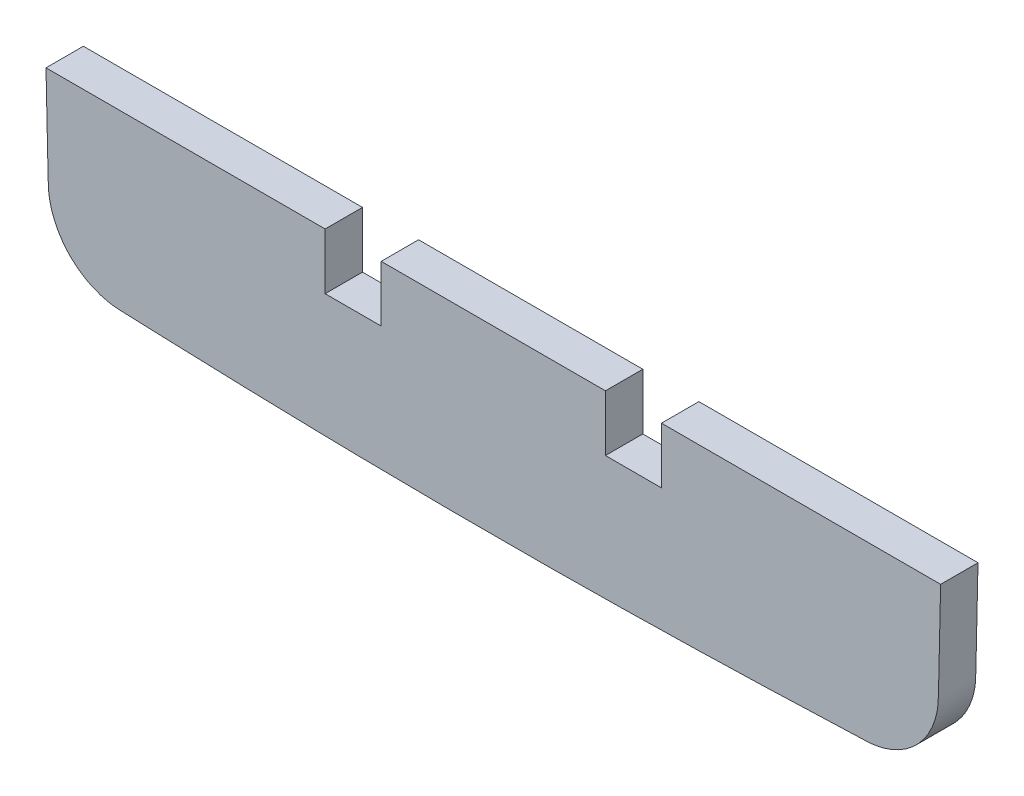
SolidWorks part; units mm, degrees
material "Beech"
ref_plane "Front Plane" through (0, 0, 0) normal (0, 0, 1) x (1, 0, 0)
ref_plane "Top Plane" through (0, 0, 0) normal (0, 1, 0) x (1, 0, 0)
ref_plane "Right Plane" through (0, 0, 0) normal (1, 0, 0) x (0, 0, -1)
sketch "Sketch1" plane through (0, 0, 0) normal (0, 0, 1) x (1, 0, 0)
  line L0 (0, 0) -> (63.5, 0) construction
  line L1 (63.5, 0) -> (63.5, 63.2554) construction
  line L2 (63.5, 0) -> (124.7026, 0) construction
  line L3 (63.5, 0) -> (63.5, -62.7074) construction
  line L4 (2.6999, -38.1) -> (124.3001, -38.1)
  line L5 (86.36, -38.1) -> (86.36, -45.72)
  line L6 (48.26, -38.1) -> (40.64, -38.1)
  line L7 (48.26, -38.1) -> (48.26, -45.72)
  line L8 (48.26, -45.72) -> (40.64, -45.72)
  line L9 (40.64, -38.1) -> (40.64, -45.72)
  line L10 (78.74, -45.72) -> (86.36, -45.72)
  line L11 (78.74, -38.1) -> (78.74, -45.72)
  line L12 (78.74, -38.1) -> (86.36, -38.1)
  spline S0 degree 3 poles (63.5, 63.2554) (72.1161, 63.2554) (81.1425, 63.1552) (90.6287, 62.9375) (95.3717, 62.8286) (100.2303, 62.6907) (105.2149, 62.5234) (107.7072, 62.4398) (110.2311, 62.3489) (112.7885, 62.2508) (113.1082, 62.2385) (113.4283, 62.2262) (113.7491, 62.2137) (113.9094, 62.2074) (114.0699, 62.2012) (114.3912, 62.1886) (114.5519, 62.1824) (114.7135, 62.1709) (115.3597, 62.1249) (116.0151, 62.0144) (117.3109, 61.6584) (117.9513, 61.4122) (118.567, 61.0968) (118.8749, 60.9391) (119.1765, 60.7646) (119.4698, 60.5741) (119.6164, 60.4788) (119.761, 60.3796) (119.9743, 60.225) (120.0448, 60.1725) (120.1496, 60.0923) (120.1843, 60.0654) (120.2362, 60.0246) (120.2535, 60.0109) (120.2794, 59.9904) (120.288, 59.9835) (120.3051, 59.9697) (120.3153, 59.9615) (120.3223, 59.9559) (120.7681, 59.5962) (121.1871, 59.1957) (121.9526, 58.3221) (122.2998, 57.8498) (122.9105, 56.8518) (123.1741, 56.3262) (123.6048, 55.2405) (123.7722, 54.6805) (124.011, 53.546) (124.0824, 52.9716) (124.1056, 52.4006) (124.1115, 52.2579) (124.1138, 52.1155) (124.1201, 51.83) (124.1233, 51.6871) (124.1265, 51.544) (124.1329, 51.2578) (124.1392, 50.9708) (124.1455, 50.683) (124.1707, 49.532) (124.1954, 48.3687) (124.2196, 47.1932) (124.268, 44.8421) (124.3143, 42.442) (124.3577, 39.9928) (124.3794, 38.7682) (124.4003, 37.5313) (124.4205, 36.2822) (124.4306, 35.6576) (124.4405, 35.03) (124.4502, 34.3993) (124.455, 34.0839) (124.4598, 33.7678) (124.4645, 33.4509) (124.4669, 33.2925) (124.4693, 33.1339) (124.4728, 32.8956) (124.4739, 32.8162) (124.4757, 32.6969) (124.4763, 32.6572) (124.4771, 32.5975) (124.4774, 32.5776) (124.4778, 32.5478) (124.478, 32.5378) (124.4782, 32.5229) (124.4783, 32.5179) (124.4784, 32.508) (124.4785, 32.5018) (124.4786, 32.498) (124.5348, 28.6259) (124.5877, 24.3084) (124.6285, 19.5453) (124.6489, 17.1637) (124.6662, 14.6708) (124.6791, 12.0667) (124.6856, 10.7646) (124.6909, 9.4347) (124.6949, 8.0771) (124.6969, 7.3983) (124.6986, 6.7125) (124.7, 6.0198) (124.7007, 5.6734) (124.7012, 5.3253) (124.7017, 4.9755) (124.702, 4.8006) (124.7022, 4.6253) (124.7025, 4.3616) (124.7026, 4.2736) (124.7028, 4.1414) (124.7028, 4.0974) (124.7029, 4.0312) (124.7029, 4.0091) (124.7029, 3.976) (124.7029, 3.965) (124.703, 3.9485) (124.703, 3.9429) (124.703, 3.9347) (124.703, 3.9319) (124.703, 3.9264) (124.703, 3.9214) (124.703, 3.9209) (124.7035, 3.3699) (124.7052, 1.9034) (124.7021, -0.4784) (124.7005, -1.6693) (124.6976, -3.089) (124.6919, -4.7373) (124.689, -5.5615) (124.6855, -6.4429) (124.681, -7.3814) (124.6787, -7.8506) (124.6762, -8.3342) (124.6735, -8.832) (124.6721, -9.0809) (124.6706, -9.3334) (124.6691, -9.5894) (124.6684, -9.7174) (124.6676, -9.8463) (124.6664, -10.0411) (124.666, -10.1062) (124.6654, -10.2042) (124.6652, -10.2369) (124.6649, -10.2861) (124.6648, -10.3025) (124.6646, -10.3272) (124.6646, -10.3354) (124.6645, -10.3477) (124.6645, -10.3518) (124.6644, -10.36) (124.6644, -10.3654) (124.6644, -10.3683) (124.6461, -13.2676) (124.6231, -15.9079) (124.5987, -18.2892) (124.5864, -19.4799) (124.5738, -20.6058) (124.5611, -21.667) (124.5548, -22.1976) (124.5485, -22.7121) (124.5421, -23.2103) (124.539, -23.4595) (124.5358, -23.7046) (124.5327, -23.9456) (124.5311, -24.0661) (124.5295, -24.1857) (124.5272, -24.3634) (124.5264, -24.4224) (124.5252, -24.5105) (124.5248, -24.5399) (124.5242, -24.5837) (124.524, -24.5983) (124.5237, -24.6202) (124.5236, -24.6275) (124.5235, -24.6384) (124.5235, -24.6421) (124.5234, -24.6494) (124.5233, -24.6513) (124.5233, -24.6567) (124.4496, -30.1549) (124.3589, -35.2827) (124.261, -40.0405) (124.2121, -42.4195) (124.1612, -44.7059) (124.1096, -46.9002) (124.0838, -47.9973) (124.0578, -49.0713) (124.0316, -50.1224) (124.0186, -50.6479) (124.0069, -51.1674) (123.9924, -51.6816) (123.9851, -51.9387) (123.9681, -52.1959) (123.9415, -52.4522) (123.9282, -52.5804) (123.9125, -52.7083) (123.8854, -52.8997) (123.8758, -52.9634) (123.8605, -53.0588) (123.8552, -53.0905) (123.8471, -53.1382) (123.8444, -53.154) (123.8402, -53.1778) (123.8388, -53.1857) (123.8367, -53.1976) (123.836, -53.2016) (123.8346, -53.2095) (123.8341, -53.2123) (123.8332, -53.2174) (123.7148, -53.876) (123.5319, -54.5285) (123.0366, -55.7896) (122.7234, -56.3983) (121.985, -57.5417) (121.5599, -58.0765) (120.6162, -59.0438) (120.0977, -59.4763) (118.9995, -60.2267) (118.4198, -60.5446) (117.2296, -61.0543) (116.6192, -61.2465) (116.0078, -61.3797) (115.7021, -61.4462) (115.3961, -61.498) (114.7871, -61.5729) (114.4845, -61.5936) (114.1842, -61.6057) (113.5835, -61.6298) (112.9862, -61.6534) (112.3923, -61.6767) (110.0169, -61.7696) (107.6958, -61.8555) (105.4273, -61.9346) (104.293, -61.9741) (103.1719, -62.0119) (102.0638, -62.048) (101.5098, -62.0661) (100.9589, -62.0837) (100.4113, -62.1009) (100.1375, -62.1095) (99.8646, -62.118) (99.5924, -62.1264) (99.4563, -62.1306) (99.3204, -62.1348) (99.1168, -62.141) (99.049, -62.1431) (98.9474, -62.1462) (98.9136, -62.1472) (98.8628, -62.1487) (98.8459, -62.1492) (98.8205, -62.15) (98.812, -62.1503) (98.7951, -62.1508) (98.7883, -62.151) (98.7782, -62.1513) (93.6295, -62.3071) (88.6269, -62.4294) (83.759, -62.5187) (81.3251, -62.5633) (78.9249, -62.5997) (76.5574, -62.6282) (75.3736, -62.6425) (74.198, -62.6547) (73.0305, -62.6651) (72.4468, -62.6702) (71.8651, -62.6749) (71.2853, -62.6791) (70.9955, -62.6812) (70.7061, -62.6832) (70.4172, -62.685) (70.2728, -62.686) (70.1285, -62.6869) (69.9122, -62.6882) (69.8401, -62.6886) (69.6961, -62.6894) (69.6254, -62.6898) (69.5521, -62.6903) (67.2067, -62.7035) (64.8341, -62.7093) (60.0428, -62.7045) (57.6274, -62.694) (52.7555, -62.6564) (50.2989, -62.6292) (47.8205, -62.5936) (46.5814, -62.5758) (45.3367, -62.5559) (44.0865, -62.5339) (43.4614, -62.5229) (42.8349, -62.5113) (42.207, -62.4992) (41.893, -62.4932) (41.5787, -62.487) (41.264, -62.4807) (41.1067, -62.4776) (40.9493, -62.4744) (40.713, -62.4696) (40.6342, -62.468) (40.516, -62.4655) (40.4766, -62.4647) (40.4175, -62.4635) (40.3978, -62.4631) (40.3584, -62.4623) (40.3365, -62.4618) (40.3189, -62.4615) (35.814, -62.3677) (31.1356, -62.2449) (26.2735, -62.091) (23.8424, -62.014) (21.3654, -61.9294) (18.8405, -61.837) (17.5781, -61.7908) (16.3037, -61.7427) (15.017, -61.6926) (14.3737, -61.6676) (13.7273, -61.6421) (13.0778, -61.6161) (12.9154, -61.6096) (12.7531, -61.6044) (12.4269, -61.5869) (12.2631, -61.5741) (11.9345, -61.54) (11.7698, -61.5188) (11.5223, -61.4807) (11.4398, -61.467) (11.316, -61.4447) (11.2747, -61.4371) (11.2128, -61.4252) (11.1921, -61.4211) (11.1612, -61.415) (11.1508, -61.4129) (11.1302, -61.4087) (11.118, -61.4062) (11.1096, -61.4045) (10.5685, -61.2934) (10.0252, -61.1357) (8.9547, -60.7201) (8.4276, -60.4612) (7.4117, -59.8452) (6.9231, -59.4883) (6.0088, -58.684) (5.584, -58.2356) (5.2013, -57.7486) (4.4358, -56.7747) (3.8388, -55.6472) (3.4688, -54.4554) (3.2839, -53.8595) (3.1536, -53.2478) (3.0788, -52.633) (3.0415, -52.3256) (3.018, -52.0175) (2.9989, -51.4031) (2.9927, -51.0952) (2.9849, -50.7859) (2.9228, -48.3115) (2.8624, -45.7608) (2.8048, -43.1337) (2.7759, -41.8201) (2.7478, -40.4875) (2.7206, -39.1357) (2.7069, -38.4598) (2.6935, -37.7791) (2.6803, -37.0936) (2.6737, -36.7509) (2.6671, -36.407) (2.6607, -36.0619) (2.6574, -35.8893) (2.6542, -35.7165) (2.6494, -35.4567) (2.6478, -35.3701) (2.6454, -35.24) (2.6446, -35.1966) (2.6434, -35.1315) (2.643, -35.1098) (2.6424, -35.0772) (2.6422, -35.0664) (2.6419, -35.0501) (2.6418, -35.0447) (2.6416, -35.0365) (2.6416, -35.0338) (2.6415, -35.0284) (2.6414, -35.0245) (2.6414, -35.0229) (2.584, -31.8888) (2.515, -27.7962) (2.4519, -22.7418) (2.4204, -20.2146) (2.3906, -17.447) (2.3654, -14.4387) (2.3529, -12.9346) (2.3415, -11.3703) (2.3318, -9.7458) (2.3269, -8.9336) (2.3225, -8.1063) (2.3185, -7.264) (2.3165, -6.8429) (2.3146, -6.418) (2.3128, -5.9893) (2.312, -5.775) (2.3111, -5.5597) (2.3103, -5.3435) (2.3099, -5.2354) (2.3095, -5.127) (2.3089, -4.9642) (2.3087, -4.9098) (2.3084, -4.8282) (2.3083, -4.801) (2.3081, -4.7465) (2.308, -4.7176) (2.308, -4.692) (2.2854, 1.849) (2.2976, 7.6491) (2.3242, 12.7049) (2.3374, 15.2328) (2.3544, 17.5748) (2.3731, 19.7307) (2.3824, 20.8086) (2.3921, 21.8401) (2.4021, 22.825) (2.4071, 23.3175) (2.4121, 23.7983) (2.4172, 24.2676) (2.4197, 24.5022) (2.4222, 24.7339) (2.4248, 24.9627) (2.426, 25.0771) (2.4273, 25.1908) (2.4292, 25.3602) (2.4299, 25.4165) (2.4308, 25.5006) (2.4311, 25.5287) (2.4316, 25.5706) (2.4318, 25.5846) (2.432, 25.6055) (2.4321, 25.6125) (2.4322, 25.623) (2.4323, 25.6264) (2.4323, 25.6334) (2.4323, 25.635) (2.4324, 25.6404) (2.4959, 31.196) (2.5777, 36.4974) (2.6703, 41.544) (2.7166, 44.0674) (2.7656, 46.527) (2.8165, 48.9231) (2.8293, 49.5221) (2.8421, 50.1172) (2.8551, 50.7083) (2.8615, 51.0038) (2.868, 51.2983) (2.8746, 51.5919) (2.8778, 51.7387) (2.8811, 51.8852) (2.8876, 52.1777) (2.8905, 52.3237) (2.8974, 52.47) (2.9252, 53.0553) (3.0035, 53.643) (3.1318, 54.2216) (3.1959, 54.511) (3.2726, 54.7981) (3.3616, 55.0816) (3.4062, 55.2233) (3.4538, 55.3642) (3.5299, 55.5739) (3.556, 55.6436) (3.5964, 55.7476) (3.6101, 55.7822) (3.6308, 55.834) (3.6378, 55.8513) (3.6483, 55.8771) (3.6518, 55.8857) (3.6589, 55.903) (3.6617, 55.9097) (3.666, 55.9202) (4.2177, 57.2536) (5.0644, 58.4838) (6.1176, 59.4692) (6.6442, 59.9619) (7.2209, 60.3951) (8.4364, 61.1263) (9.0751, 61.4232) (10.378, 61.872) (11.042, 62.0255) (11.7012, 62.1118) (12.0307, 62.1549) (12.3587, 62.1788) (13.0096, 62.2043) (13.3343, 62.217) (13.6583, 62.2295) (14.9545, 62.2796) (16.2396, 62.3278) (17.5139, 62.3741) (20.0625, 62.4667) (22.568, 62.5516) (25.032, 62.6288) (26.264, 62.6674) (27.4856, 62.7041) (28.6971, 62.7389) (29.3028, 62.7563) (29.906, 62.7733) (30.5067, 62.7897) (30.807, 62.798) (31.1068, 62.8061) (31.4058, 62.8141) (31.5554, 62.8181) (31.7047, 62.822) (31.9286, 62.8279) (32.0032, 62.8299) (32.115, 62.8328) (32.1522, 62.8338) (32.2081, 62.8353) (32.2267, 62.8358) (32.2546, 62.8365) (32.2639, 62.8367) (32.2826, 62.8372) (32.2905, 62.8374) (32.3012, 62.8377) (43.1888, 63.1215) (53.5619, 63.2554) (63.5, 63.2554) (72.1161, 63.2554) (81.1425, 63.1552) knots -0.004831 0 0 0 0.004831 0.004831 0.004831 0.009662 0.009662 0.009662 0.014493 0.014493 0.014493 0.019324 0.019324 0.019324 0.024155 0.024155 0.028986 0.028986 0.028986 0.033816 0.033816 0.038647 0.038647 0.038647 0.043478 0.043478 0.043478 0.048309 0.048309 0.05314 0.05314 0.057971 0.057971 0.062802 0.062802 0.067633 0.067633 0.072464 0.072464 0.072464 0.077295 0.077295 0.082126 0.082126 0.086957 0.086957 0.091787 0.091787 0.096618 0.096618 0.096618 0.101449 0.101449 0.10628 0.10628 0.10628 0.111111 0.111111 0.111111 0.115942 0.115942 0.115942 0.120773 0.120773 0.120773 0.125604 0.125604 0.125604 0.130435 0.130435 0.130435 0.135266 0.135266 0.135266 0.140097 0.140097 0.144928 0.144928 0.149758 0.149758 0.154589 0.154589 0.15942 0.15942 0.164251 0.164251 0.169082 0.169082 0.169082 0.173913 0.173913 0.173913 0.178744 0.178744 0.178744 0.183575 0.183575 0.183575 0.188406 0.188406 0.188406 0.193237 0.193237 0.193237 0.198068 0.198068 0.202899 0.202899 0.207729 0.207729 0.21256 0.21256 0.217391 0.217391 0.222222 0.222222 0.227053 0.227053 0.231884 0.231884 0.231884 0.236715 0.236715 0.236715 0.241546 0.241546 0.241546 0.246377 0.246377 0.246377 0.251208 0.251208 0.251208 0.256039 0.256039 0.256039 0.26087 0.26087 0.2657 0.2657 0.270531 0.270531 0.275362 0.275362 0.280193 0.280193 0.285024 0.285024 0.289855 0.289855 0.289855 0.294686 0.294686 0.294686 0.299517 0.299517 0.299517 0.304348 0.304348 0.304348 0.309179 0.309179 0.309179 0.31401 0.31401 0.318841 0.318841 0.323671 0.323671 0.328502 0.328502 0.333333 0.333333 0.338164 0.338164 0.342995 0.342995 0.342995 0.347826 0.347826 0.347826 0.352657 0.352657 0.352657 0.357488 0.357488 0.357488 0.362319 0.362319 0.362319 0.36715 0.36715 0.36715 0.371981 0.371981 0.376812 0.376812 0.381643 0.381643 0.386473 0.386473 0.391304 0.391304 0.396135 0.396135 0.400966 0.400966 0.400966 0.405797 0.405797 0.410628 0.410628 0.415459 0.415459 0.42029 0.42029 0.425121 0.425121 0.429952 0.429952 0.429952 0.434783 0.434783 0.439614 0.439614 0.439614 0.444444 0.444444 0.444444 0.449275 0.449275 0.449275 0.454106 0.454106 0.454106 0.458937 0.458937 0.458937 0.463768 0.463768 0.463768 0.468599 0.468599 0.47343 0.47343 0.478261 0.478261 0.483092 0.483092 0.487923 0.487923 0.492754 0.492754 0.492754 0.497585 0.497585 0.497585 0.502415 0.502415 0.502415 0.507246 0.507246 0.507246 0.512077 0.512077 0.512077 0.516908 0.516908 0.516908 0.521739 0.521739 0.52657 0.52657 0.531401 0.531401 0.531401 0.536232 0.536232 0.541063 0.541063 0.545894 0.545894 0.545894 0.550725 0.550725 0.550725 0.555556 0.555556 0.555556 0.560386 0.560386 0.560386 0.565217 0.565217 0.570048 0.570048 0.574879 0.574879 0.57971 0.57971 0.584541 0.584541 0.584541 0.589372 0.589372 0.589372 0.594203 0.594203 0.594203 0.599034 0.599034 0.599034 0.603865 0.603865 0.603865 0.608696 0.608696 0.613527 0.613527 0.618357 0.618357 0.623188 0.623188 0.628019 0.628019 0.63285 0.63285 0.637681 0.637681 0.642512 0.642512 0.642512 0.647343 0.647343 0.652174 0.652174 0.657005 0.657005 0.661836 0.661836 0.661836 0.666667 0.666667 0.666667 0.671498 0.671498 0.671498 0.676329 0.676329 0.681159 0.681159 0.681159 0.68599 0.68599 0.68599 0.690821 0.690821 0.690821 0.695652 0.695652 0.695652 0.700483 0.700483 0.700483 0.705314 0.705314 0.710145 0.710145 0.714976 0.714976 0.719807 0.719807 0.724638 0.724638 0.729469 0.729469 0.7343 0.7343 0.73913 0.73913 0.73913 0.743961 0.743961 0.743961 0.748792 0.748792 0.748792 0.753623 0.753623 0.753623 0.758454 0.758454 0.758454 0.763285 0.763285 0.763285 0.768116 0.768116 0.768116 0.772947 0.772947 0.777778 0.777778 0.782609 0.782609 0.78744 0.78744 0.78744 0.792271 0.792271 0.792271 0.797101 0.797101 0.797101 0.801932 0.801932 0.801932 0.806763 0.806763 0.806763 0.811594 0.811594 0.811594 0.816425 0.816425 0.821256 0.821256 0.826087 0.826087 0.830918 0.830918 0.835749 0.835749 0.84058 0.84058 0.845411 0.845411 0.845411 0.850242 0.850242 0.850242 0.855072 0.855072 0.855072 0.859903 0.859903 0.859903 0.864734 0.864734 0.864734 0.869565 0.869565 0.874396 0.874396 0.874396 0.879227 0.879227 0.879227 0.884058 0.884058 0.884058 0.888889 0.888889 0.89372 0.89372 0.898551 0.898551 0.903382 0.903382 0.908213 0.908213 0.913043 0.913043 0.913043 0.917874 0.917874 0.917874 0.922705 0.922705 0.927536 0.927536 0.932367 0.932367 0.932367 0.937198 0.937198 0.942029 0.942029 0.942029 0.94686 0.94686 0.94686 0.951691 0.951691 0.951691 0.956522 0.956522 0.956522 0.961353 0.961353 0.961353 0.966184 0.966184 0.966184 0.971014 0.971014 0.975845 0.975845 0.980676 0.980676 0.985507 0.985507 0.990338 0.990338 0.995169 0.995169 0.995169 1 1 1 1.004831 1.004831 1.004831 only from (63.5, 63.2554) to (63.5, 63.2554)
  point P4 (2.2976, -0.1992)
  dimension "D1" = 63.2554
  dimension "D2" = 63.5
  dimension "D3" = 61.2026
  dimension "D4" = 62.7074
  dimension "D5" = 38.1
  dimension "D6" = 7.62
  dimension "D7" = 7.62
  dimension "D8" = 15.24
extrude "Boss-Extrude1" add sketch "Sketch1" along normal blind 5.08 contours S0 L4 L5 L10 L11 L7 L8 L9
